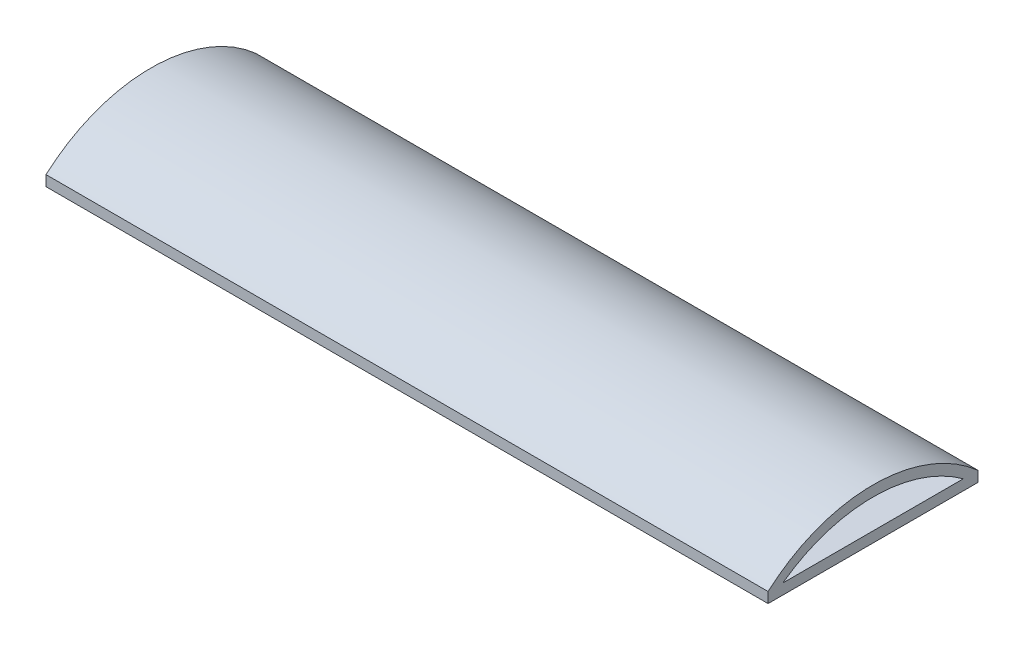
SolidWorks part; units mm, degrees
ref_plane "Спереди" through (0, 0, 0) normal (0, 0, 1) x (1, 0, 0)
ref_plane "Сверху" through (0, 0, 0) normal (0, 1, 0) x (1, 0, 0)
ref_plane "Справа" through (0, 0, 0) normal (1, 0, 0) x (0, 0, -1)
sketch "Эскиз1" plane through (0, 0, 0) normal (0, 1, 0) x (1, 0, 0)
  line L1 (17.2, 5) -> (-17.2, 5)
  line L2 (17.2, 5) -> (17.2, -5)
  line L3 (17.2, -5) -> (-17.2, -5)
  line L4 (-17.2, 5) -> (-17.2, -5)
  line L5 (17.2, 5) -> (-17.2, -5) construction
  line L6 (17.2, -5) -> (-17.2, 5) construction
  point P0 (0, 0)
  dimension "D1" = 34.4
  dimension "D2" = 10
extrude "Бобышка-Вытянуть1" add sketch "Эскиз1" along normal blind 0.5
sketch "Эскиз2" plane through (-17.2, 0, 0) normal (-1, 0, 0) x (0, 0, 1)
  line L0 (-5, 0.5) -> (5, 0.5) construction
  line L1 (-5, 0.5) -> (-4.3, 0.5)
  line L2 (5, 0.5) -> (4.3, 0.5)
  line L4 (-5, 0) -> (5, 0)
  line L5 (5, 0) -> (5, 0.5)
  line L6 (5, 0.5) -> (-5, 0.5)
  line L7 (-5, 0.5) -> (-5, 0)
  line L8 (-5, 0) -> (5, 0)
  line L9 (5, 0) -> (5, 0.5)
  line L11 (-5, 0.5) -> (-5, 0)
  arc A0 (-5, 0.5) -> (5, 0.5) centre (0, -5.125) cw
  arc A1 (-4.3, 0.5) -> (4.3, 0.5) centre (0, -5.4036) cw
  point P0 (0, 2.4)
  point P9 (0, 1.9)
  point P10 (-4.3, 0.5)
  point P11 (4.3, 0.5)
  line M3 (5, 0.5) -> (-5, 0.5)
  dimension "D1" = 2.4
  dimension "D3" = 0.5
  dimension "D4" = 0.7
  dimension "D5" = 0.7
  dimension "D2" = 0
extrude "Бобышка-Вытянуть2" add sketch "Эскиз2" against normal through all contours A1 A0 M3
